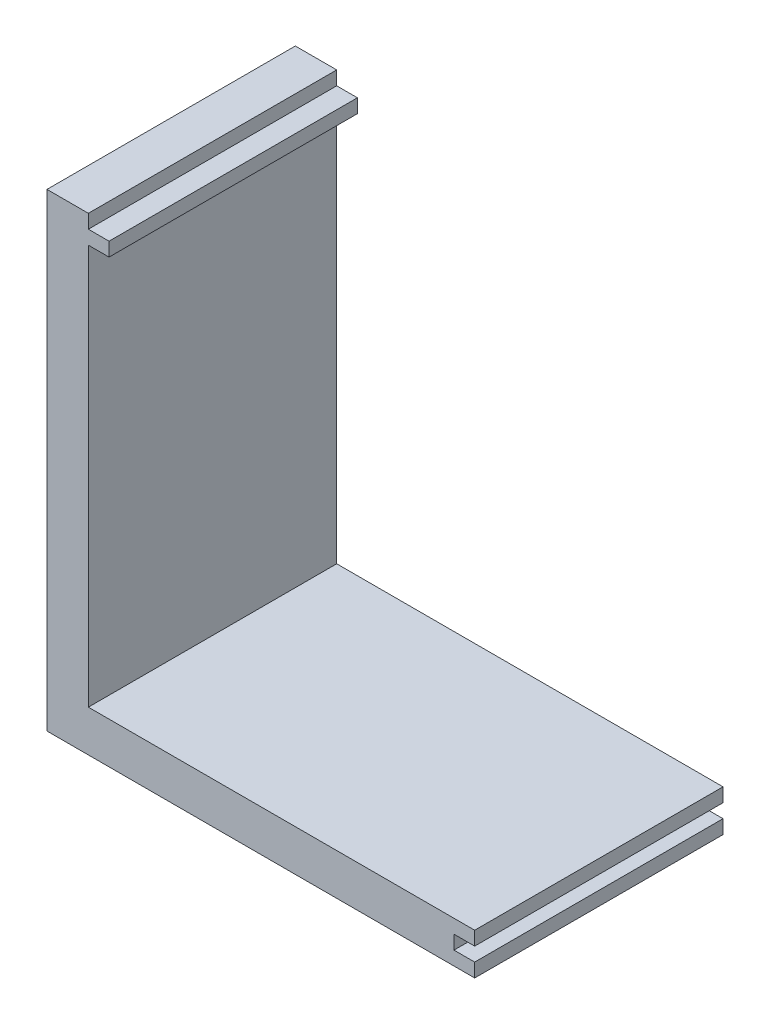
SolidWorks part; units mm, degrees
ref_plane "Plan de face" through (0, 0, 0) normal (1, 0, 0) x (0, 1, 0)
ref_plane "Plan de dessus" through (0, 0, 0) normal (0, 0, 1) x (0, 1, 0)
ref_plane "Plan de droite" through (0, 0, 0) normal (0, 1, 0) x (-1, 0, 0)
sketch "Esquisse1" plane through (0, 0, 0) normal (0, 0, 1) x (0, 1, 0)
  line L0 (0, 0) -> (31, 0)
  line L2 (0, 0) -> (0, -28)
  line L3 (0, -28) -> (-3, -28)
  line L4 (-3, 0) -> (-3, -28)
  line L6 (-3, 0) -> (-3, 3)
  line L7 (-3, 3) -> (31, 3)
  line L8 (31, 0) -> (31, 3)
  dimension "D1" = 28
  dimension "D2" = 3
  dimension "D3" = 31
extrude "Boss_Extrude_Equerre" add sketch "Esquisse1" along normal blind 18
sketch "Esquisse2" plane through (0, 0, 18) normal (0, 0, 1) x (1, 0, 0)
  line L0 (28, -3) -> (28, 0) construction
  line L1 (26.5, -2) -> (29.5, -2)
  line L2 (26.5, -2) -> (26.5, -1)
  line L3 (26.5, -1) -> (29.5, -1)
  line L4 (29.5, -2) -> (29.5, -1)
  line L5 (26.5, -2) -> (29.5, -1) construction
  line L6 (26.5, -1) -> (29.5, -2) construction
  point P0 (28, -1.5)
  dimension "D1" = 1
  dimension "D2" = 3
extrude "Enlèv. mat.-Extru.1" cut sketch "Esquisse2" against normal through all
sketch "Esquisse3" plane through (0, 0, 18) normal (0, 0, 1) x (1, 0, 0)
  line L0 (0, 0) -> (0, 31) construction
  line L1 (0, 31) -> (-3, 31) construction
  line L2 (0, 29) -> (0, 30)
  line L6 (1.5, 30) -> (1.5, 29)
  line L7 (0, 30) -> (1.5, 30)
  line L8 (0, 29) -> (1.5, 29)
  point P0 (0, 29.5)
  point P5 (0, 29.5)
  dimension "D1" = 1.5
  dimension "D2" = 1
  dimension "D3" = 1.5
extrude "Boss.-Extru.1" add sketch "Esquisse3" against normal through all
equation "\"Plaque_L\"=\"Cavite_L\"+\"Cavite_E\"'longueur plaque"
equation "\"Plaque_H\"= \"Cavite_L\"+\"Cavite_E\"'largeur plaque"
equation "\"Plaque_E\"= 2mm'épaisseur plaque superieure et inferieure"
equation "\"Trou_R\"= 1.2mm'rayon perforation base"
equation "\"Trou_dx\"= 4mm'distance entre trou sur x"
equation "\"Trou-dy\"= 4mm'distance entre trou sur y"
equation "\"Cavite_H\"= 18mm'hauteur cavité"
equation "\"Cavite_L\"=\"Cavite_largeur\"+\"Cavite_E\"'longueur cavité"
equation "\"Cavite_E\"= 3mm'épaisseur cavité"
equation "\"Offset_Z\"= 0mm"
equation "\"D2@Esquisse1\"=\"Cavite_E\""
equation "\"D3@Esquisse1\"=\"Cavite_L\""
equation "\"D1@Esquisse1\"=\"Cavite_largeur\""
equation "\"Cavite_largeur\"= 28mm'largeur cavité"
equation "\"Vis_Diam\"= 1.6mm"
equation "\"Offset_Bord\"= \"Cavite_E\" / 2"
equation "\"Vis_Long\"= 5mm"
equation "\"Perc_Passage\"= 1.8mm"
equation "\"Perc_Taraud\"= 1.3mm"
equation "\"Fraisure_Diam\"= 3mm"
equation "\"Fraisure_Prof\"= 1mm"
equation "\"Offset_hauteur_vis1\"= \"Cavite_E\""
equation "\"Offset_hauteur_vis2\"= \"Cavite_H\" - \"Cavite_E\""
equation "\"Perc_Profondeur\"= 8mm"
equation "\"Taraud_Profondeur\"= \"Cavite_E\""
equation "\"d\"= 0.002"
equation "\"N_Plaque\"= 7"
equation "\"N_Cavite\"= 6"
equation "\"Offset_cavite\"= \"Cavite_E\" / 2"
equation "\"H_total\"=113mm'122-2*2"
equation "\"espace_vis\"=22.6mm'"
equation "\"Largeur_equerre_enveloppe\"=\"Cavite_L\"+\"Cavite_E\""
equation "\"Enveloppe_E\"=5mm"
equation "\"Offset_Enveloppe\"= \"Enveloppe_E\" / 2"
equation "\"Longueur_equerre_enveloppe\"=\"Cavite_L\"+\"Cavite_E\"+\"Enveloppe_E\""
equation "\"largeur_plaque_enveloppe\"=\"Longueur_equerre_enveloppe\"+\"Enveloppe_E\""
equation "\"D1@Boss_Extrude_Equerre\"=\"Cavite_H\""
